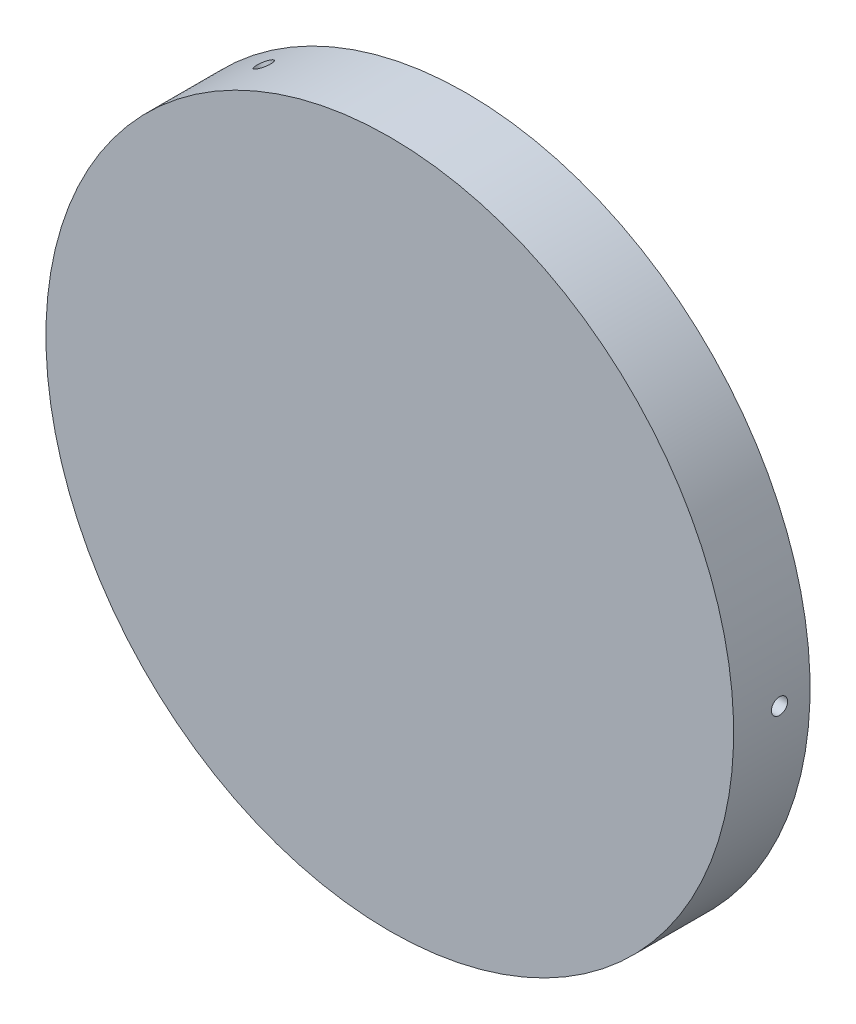
SolidWorks part; units mm, degrees
material "Delrin 2700 NC010, Low Viscosity Acetal Copolymer (SS)"
ref_plane "Front Plane" through (0, 0, 0) normal (0, 0, 1) x (1, 0, 0)
ref_plane "Top Plane" through (0, 0, 0) normal (0, 1, 0) x (1, 0, 0)
ref_plane "Right Plane" through (0, 0, 0) normal (1, 0, 0) x (0, 0, -1)
sketch "Sketch1" plane through (0, 0, 0) normal (1, 0, 0) x (0, 0, -1)
  line L0 (0, 0) -> (-6.7945, 0) construction
  line L1 (-6.7945, 0) -> (-11.43, 0)
  line L2 (-11.43, 0) -> (-11.43, 85.725)
  line L3 (-11.43, 85.725) -> (7.62, 85.725)
  line L4 (7.62, 85.725) -> (7.62, 76.2)
  line L5 (7.62, 76.2) -> (-6.7945, 76.2)
  line L6 (-6.7945, 76.2) -> (-6.7945, 0)
  dimension "D1" = 7.62
  dimension "D2" = 14.4145
  dimension "D3" = 19.05
  dimension "D4" = 76.2
  dimension "D5" = 85.725
revolve "Revolve1" add sketch "Sketch1" angle 360 about L0
ref_plane "Plane1" through (85.725, 0, 0) normal (1, 0, 0) x (0, 0, -1)
hole_wizard "#10-32 Tapped Hole1" positions "Sketch6" profile "Sketch8" tap size "#10-32" standard "ANSI Inch"
sketch "Sketch6" plane through (85.725, 0, 0) normal (1, 0, 0) x (0, 0, -1)
  point P0 (0, 0)
sketch "Sketch8" plane through (85.725, 0, 0) normal (0, 1, 0) x (0, 0, -1)
  line L0 (0, 0) -> (0, 86.9373)
  line L1 (0, 86.9373) -> (2.0193, 85.724)
  line L2 (2.0193, 85.724) -> (2.0193, 0)
  line L5 (2.0193, 0) -> (0, 0)
  line L10 (0, 86.9373) -> (-2.0193, 85.724) construction
  line L11 (0, -6.35) -> (0, 107.95) construction
  dimension "Tap Drill Dia." = 4.0386
  dimension "Tap Drill Depth" = 85.724
  dimension "Drill Angle" = 118
cosmetic thread "Hole Thread2" parameters "D1"=9.652, "D2"=4.826
pattern_circular "CirPattern1" count 3 over 360 about axis through (0, 0, 0) along (0, 0, -1) of "#10-32 Tapped Hole1"
